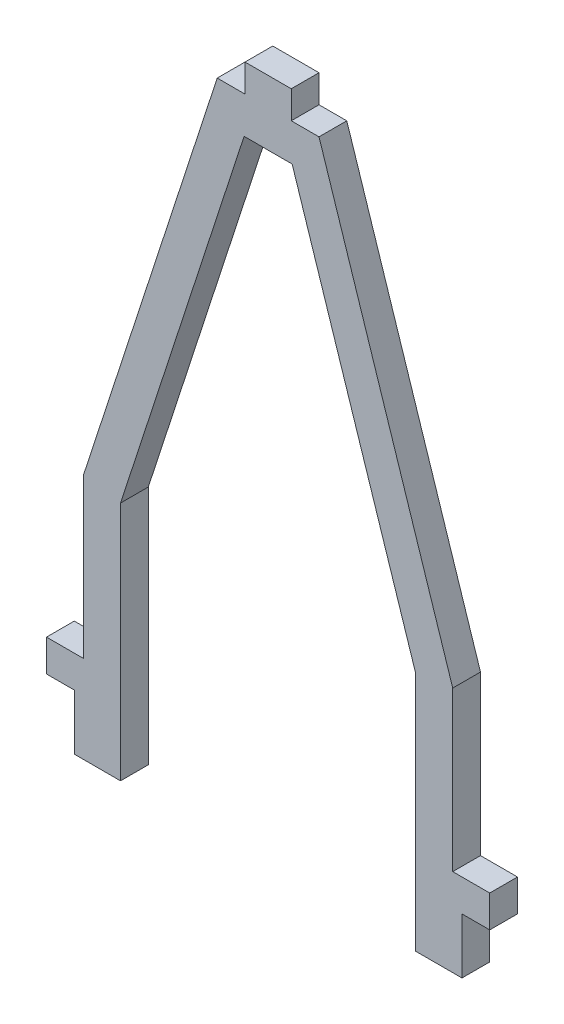
SolidWorks part; units mm, degrees
material "Custom Plastic"
ref_plane "Front Plane" through (0, 0, 0) normal (0, 0, 1) x (1, 0, 0)
ref_plane "Top Plane" through (0, 0, 0) normal (0, 1, 0) x (1, 0, 0)
ref_plane "Right Plane" through (0, 0, 0) normal (1, 0, 0) x (0, 0, -1)
sketch "Sketch1" plane through (0, 0, 0) normal (0, 0, 1) x (1, 0, 0)
  line L20 (-6.3839, -69.0934) -> (-6.3839, -43.0934)
  line L38 (-6.3839, -43.0934) -> (6.9701, -2.0934)
  line L39 (6.9701, -2.0934) -> (12.1621, -2.0934)
  line L40 (9.5661, -2.0934) -> (9.5661, 4.9066) construction
  line L41 (7.0661, 4.9066) -> (12.0661, 4.9066)
  line L42 (12.0661, 4.9066) -> (12.0661, 1.9066)
  line L44 (4.0661, 1.9066) -> (-10.3839, -42.4584)
  line L45 (-10.3839, -42.4584) -> (-10.3839, -59.6388)
  line L46 (-10.3839, -59.6388) -> (-14.3839, -59.6388)
  line L47 (-14.3839, -59.6388) -> (-14.3839, -63.0934)
  line L48 (-14.3839, -63.0934) -> (-11.3839, -63.0934)
  line L49 (-11.3839, -63.0934) -> (-11.3839, -69.0934)
  line L50 (-11.3839, -69.0934) -> (-6.3839, -69.0934)
  line L51 (-10.3839, -42.4584) -> (-6.3839, -43.0934) construction
  line L52 (4.0661, 1.9066) -> (6.9701, -2.0934) construction
  line L53 (15.0661, 1.9066) -> (12.1621, -2.0934) construction
  line L54 (29.5161, -42.4584) -> (25.5161, -43.0934) construction
  line L55 (30.5161, -69.0934) -> (25.5161, -69.0934)
  line L56 (30.5161, -63.0934) -> (30.5161, -69.0934)
  line L57 (33.5161, -63.0934) -> (30.5161, -63.0934)
  line L58 (33.5161, -59.6388) -> (33.5161, -63.0934)
  line L59 (29.5161, -59.6388) -> (33.5161, -59.6388)
  line L60 (29.5161, -42.4584) -> (29.5161, -59.6388)
  line L61 (15.0661, 1.9066) -> (29.5161, -42.4584)
  line L63 (7.0661, 4.9066) -> (7.0661, 1.9066)
  line L64 (25.5161, -43.0934) -> (12.1621, -2.0934)
  line L65 (25.5161, -69.0934) -> (25.5161, -43.0934)
  line L66 (4.0661, 1.9066) -> (7.0661, 1.9066)
  line L67 (12.0661, 1.9066) -> (15.0661, 1.9066)
  point P28 (7.0661, 3.4066)
  dimension "D1" = 6
  dimension "D2" = 3
  dimension "D3" = 4
  dimension "D4" = 5
  dimension "D5" = 4
  dimension "D6" = 65
  dimension "D7" = 41.9
  dimension "D8" = 20
  dimension "D9" = 4
  dimension "D10" = 5
  dimension "D11" = 3
  dimension "D12" = 3
extrude "Boss-Extrude1" add sketch "Sketch1" along normal blind 3
